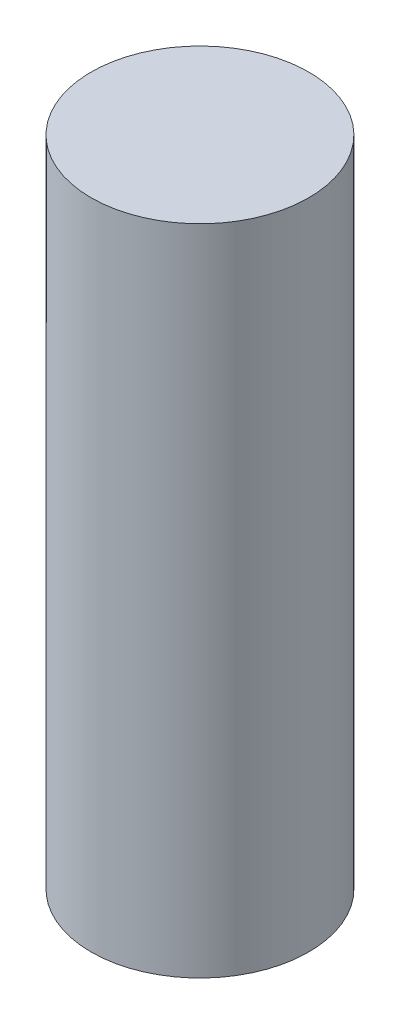
SolidWorks part; units mm, degrees
ref_plane "Front Plane" through (0, 0, 0) normal (0, 0, 1) x (1, 0, 0)
ref_plane "Top Plane" through (0, 0, 0) normal (0, 1, 0) x (1, 0, 0)
ref_plane "Right Plane" through (0, 0, 0) normal (1, 0, 0) x (0, 0, -1)
sketch "Sketch1" plane through (0, 0, 0) normal (0, 1, 0) x (1, 0, 0)
  circle A0 centre (0, 0) radius 1.5875
  dimension "D1" = 3.175
extrude "Boss-Extrude1" add sketch "Sketch1" along normal blind 9.525
hole_wizard "5/64 (0.07813) Diameter Hole1" positions "Sketch5" profile "Sketch4" hole size "5/64" standard "ANSI Inch"
sketch "Sketch5" plane through (0, 0, 0) normal (0, -1, 0) x (-1, 0, 0)
  point P0 (0, 0)
sketch "Sketch4" plane through (0, 0, 0) normal (1, 0, 0) x (0, 0, -1)
  line L0 (0, 0) -> (0, 5.6762)
  line L1 (0, 5.6762) -> (0.9923, 5.08)
  line L2 (0.9923, 5.08) -> (0.9923, 0)
  line L5 (0.9923, 0) -> (0, 0)
  line L10 (0, 5.6762) -> (-0.9923, 5.08) construction
  line L11 (0, -6.35) -> (0, 107.95) construction
  dimension "Hole Dia." = 1.9845
  dimension "Hole Depth" = 5.08
  dimension "Drill Angle" = 118
